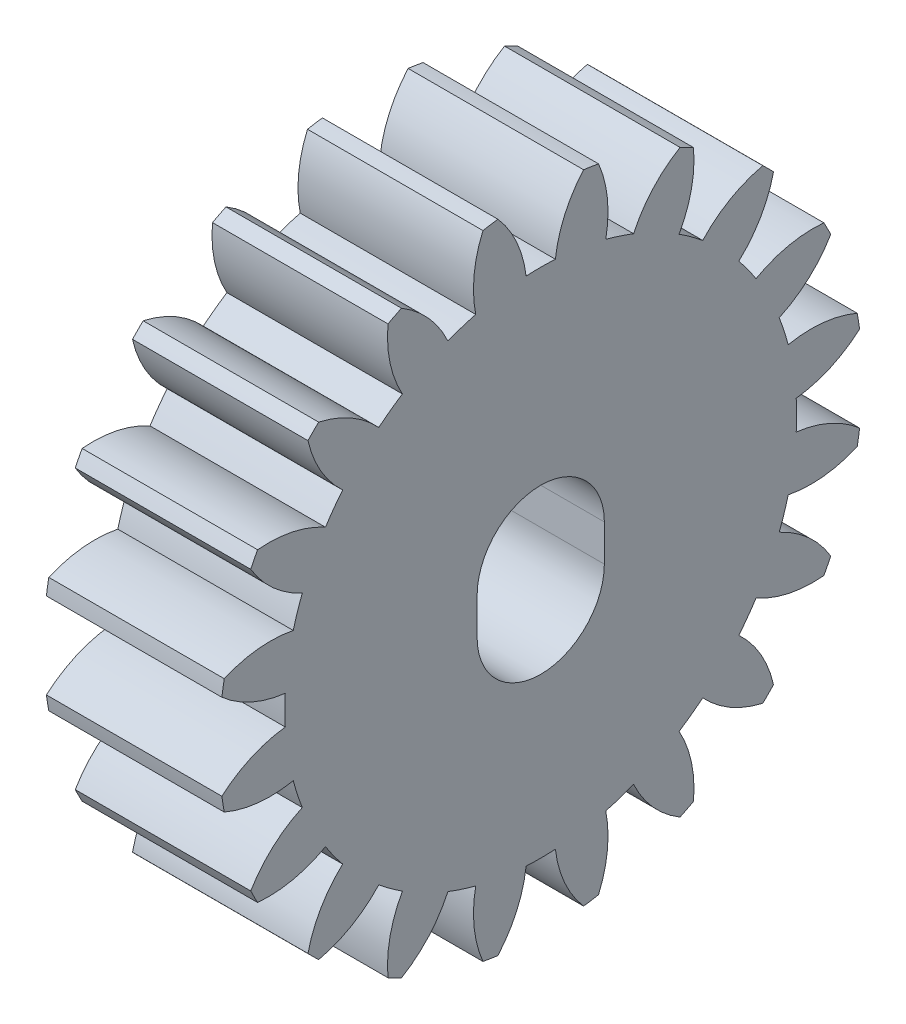
SolidWorks part; units mm, degrees
ref_plane "Спереди" through (0, 0, 0) normal (0, 0, 1) x (1, 0, 0)
ref_plane "Сверху" through (0, 0, 0) normal (0, 1, 0) x (1, 0, 0)
ref_plane "Справа" through (0, 0, 0) normal (1, 0, 0) x (0, 0, -1)
ref_plane "Плоскость4" through (0.2049, 0, 0) normal (1, 0, 0) x (0, 0, -1)
sketch "Эскиз1" plane through (0.2049, 3.1521, 1.205) normal (1, 0, 0) x (0, 0, -1)
  line L0 (1.205, -3.0337) -> (1.205, -4.2837) construction
  line L3 (3.38, -3.0337) -> (3.38, -4.2837)
  line L4 (-0.97, -3.0337) -> (-0.97, -4.2837)
  arc A1 (-9.697, -1.6872) -> (-7.5297, -2.6522) centre (-7.0595, 1.3201) ccw
  arc A2 (-7.5297, -2.6522) -> (-7.5297, -3.6521) centre (1.205, -3.1521) ccw
  arc A3 (-7.5297, -3.6521) -> (-9.697, -4.6171) centre (-7.0595, -7.6243) ccw
  arc A4 (-9.697, -4.6171) -> (-9.6161, -5.1278) centre (1.205, -3.1521) ccw
  arc A5 (-9.6161, -5.1278) -> (-7.2567, -5.3758) centre (-8.0369, -1.4527) ccw
  arc A6 (-7.2567, -5.3758) -> (-6.9477, -6.3268) centre (1.205, -3.1521) ccw
  arc A7 (-6.9477, -6.3268) -> (-8.7107, -7.9143) centre (-5.273, -9.9593) ccw
  arc A8 (-8.7107, -7.9143) -> (-8.476, -8.375) centre (1.205, -3.1521) ccw
  arc A9 (-8.476, -8.375) -> (-6.1553, -7.8818) centre (-8.1098, -4.3918) ccw
  arc A10 (-6.1553, -7.8818) -> (-5.5676, -8.6907) centre (1.205, -3.1521) ccw
  arc A11 (-5.5676, -8.6907) -> (-6.7538, -10.7453) centre (-2.8524, -11.6279) ccw
  arc A12 (-6.7538, -10.7453) -> (-6.3882, -11.111) centre (1.205, -3.1521) ccw
  arc A13 (-6.3882, -11.111) -> (-4.3335, -9.9248) centre (-7.2708, -7.2095) ccw
  arc A14 (-4.3335, -9.9248) -> (-3.5247, -10.5125) centre (1.205, -3.1521) ccw
  arc A15 (-3.5247, -10.5125) -> (-4.0178, -12.8331) centre (-0.0346, -12.4669) ccw
  arc A16 (-4.0178, -12.8331) -> (-3.5571, -13.0679) centre (1.205, -3.1521) ccw
  arc A17 (-3.5571, -13.0679) -> (-1.9696, -11.3048) centre (-5.6021, -9.6301) ccw
  arc A18 (-1.9696, -11.3048) -> (-1.0187, -11.6138) centre (1.205, -3.1521) ccw
  arc A19 (-1.0187, -11.6138) -> (-0.7706, -13.9733) centre (2.9045, -12.3941) ccw
  arc A20 (-0.7706, -13.9733) -> (-0.2599, -14.0541) centre (1.205, -3.1521) ccw
  arc A21 (-0.2599, -14.0541) -> (0.7051, -11.8868) centre (-3.2672, -11.4166) ccw
  arc A22 (0.7051, -11.8868) -> (1.705, -11.8868) centre (1.205, -3.1521) ccw
  arc A23 (1.705, -11.8868) -> (2.67, -14.0541) centre (5.6772, -11.4166) ccw
  arc A24 (2.67, -14.0541) -> (3.1807, -13.9733) centre (1.205, -3.1521) ccw
  arc A25 (3.1807, -13.9733) -> (3.4287, -11.6138) centre (-0.4944, -12.3941) ccw
  arc A26 (3.4287, -11.6138) -> (4.3797, -11.3048) centre (1.205, -3.1521) ccw
  arc A27 (4.3797, -11.3048) -> (5.9672, -13.0679) centre (8.0122, -9.6301) ccw
  arc A28 (5.9672, -13.0679) -> (6.4279, -12.8331) centre (1.205, -3.1521) ccw
  arc A29 (6.4279, -12.8331) -> (5.9347, -10.5125) centre (2.4447, -12.4669) ccw
  arc A30 (5.9347, -10.5125) -> (6.7436, -9.9248) centre (1.205, -3.1521) ccw
  arc A31 (6.7436, -9.9248) -> (8.7982, -11.111) centre (9.6809, -7.2095) ccw
  arc A32 (8.7982, -11.111) -> (9.1639, -10.7453) centre (1.205, -3.1521) ccw
  arc A33 (9.1639, -10.7453) -> (7.9777, -8.6907) centre (5.2625, -11.6279) ccw
  arc A34 (7.9777, -8.6907) -> (8.5654, -7.8818) centre (1.205, -3.1521) ccw
  arc A35 (8.5654, -7.8818) -> (10.886, -8.375) centre (10.5198, -4.3918) ccw
  arc A36 (10.886, -8.375) -> (11.1208, -7.9143) centre (1.205, -3.1521) ccw
  arc A37 (11.1208, -7.9143) -> (9.3577, -6.3268) centre (7.683, -9.9593) ccw
  arc A38 (9.3577, -6.3268) -> (9.6667, -5.3758) centre (1.205, -3.1521) ccw
  arc A39 (9.6667, -5.3758) -> (12.0262, -5.1278) centre (10.447, -1.4527) ccw
  arc A40 (12.0262, -5.1278) -> (12.107, -4.6171) centre (1.205, -3.1521) ccw
  arc A41 (12.107, -4.6171) -> (9.9397, -3.6521) centre (9.4695, -7.6243) ccw
  arc A42 (9.9397, -3.6521) -> (9.9397, -2.6522) centre (1.205, -3.1521) ccw
  arc A43 (9.9397, -2.6522) -> (12.107, -1.6872) centre (9.4695, 1.3201) ccw
  arc A44 (12.107, -1.6872) -> (12.0262, -1.1765) centre (1.205, -3.1521) ccw
  arc A45 (12.0262, -1.1765) -> (9.6667, -0.9284) centre (10.447, -4.8516) ccw
  arc A46 (9.6667, -0.9284) -> (9.3577, 0.0225) centre (1.205, -3.1521) ccw
  arc A47 (9.3577, 0.0225) -> (11.1208, 1.61) centre (7.683, 3.655) ccw
  arc A48 (11.1208, 1.61) -> (10.886, 2.0707) centre (1.205, -3.1521) ccw
  arc A49 (10.886, 2.0707) -> (8.5654, 1.5776) centre (10.5198, -1.9125) ccw
  arc A50 (8.5654, 1.5776) -> (7.9777, 2.3865) centre (1.205, -3.1521) ccw
  arc A51 (7.9777, 2.3865) -> (9.1639, 4.4411) centre (5.2625, 5.3237) ccw
  arc A52 (9.1639, 4.4411) -> (8.7982, 4.8067) centre (1.205, -3.1521) ccw
  arc A53 (8.7982, 4.8067) -> (6.7436, 3.6206) centre (9.6809, 0.9053) ccw
  arc A54 (6.7436, 3.6206) -> (5.9347, 4.2082) centre (1.205, -3.1521) ccw
  arc A55 (5.9347, 4.2082) -> (6.4279, 6.5289) centre (2.4447, 6.1627) ccw
  arc A56 (6.4279, 6.5289) -> (5.9672, 6.7636) centre (1.205, -3.1521) ccw
  arc A57 (5.9672, 6.7636) -> (4.3797, 5.0006) centre (8.0122, 3.3259) ccw
  arc A58 (4.3797, 5.0006) -> (3.4287, 5.3096) centre (1.205, -3.1521) ccw
  arc A59 (3.4287, 5.3096) -> (3.1807, 7.669) centre (-0.4944, 6.0899) ccw
  arc A60 (3.1807, 7.669) -> (2.67, 7.7499) centre (1.205, -3.1521) ccw
  arc A61 (2.67, 7.7499) -> (1.705, 5.5826) centre (5.6772, 5.1124) ccw
  arc A62 (1.705, 5.5826) -> (0.7051, 5.5826) centre (1.205, -3.1521) ccw
  arc A63 (0.7051, 5.5826) -> (-0.2599, 7.7499) centre (-3.2672, 5.1124) ccw
  arc A64 (-0.2599, 7.7499) -> (-0.7706, 7.669) centre (1.205, -3.1521) ccw
  arc A65 (-0.7706, 7.669) -> (-1.0187, 5.3096) centre (2.9045, 6.0899) ccw
  arc A66 (-1.0187, 5.3096) -> (-1.9696, 5.0006) centre (1.205, -3.1521) ccw
  arc A67 (-1.9696, 5.0006) -> (-3.5571, 6.7636) centre (-5.6021, 3.3259) ccw
  arc A68 (-3.5571, 6.7636) -> (-4.0178, 6.5289) centre (1.205, -3.1521) ccw
  arc A69 (-4.0178, 6.5289) -> (-3.5247, 4.2082) centre (-0.0346, 6.1627) ccw
  arc A70 (-3.5247, 4.2082) -> (-4.3335, 3.6206) centre (1.205, -3.1521) ccw
  arc A71 (-4.3335, 3.6206) -> (-6.3882, 4.8067) centre (-7.2708, 0.9053) ccw
  arc A72 (-6.3882, 4.8067) -> (-6.7538, 4.4411) centre (1.205, -3.1521) ccw
  arc A73 (-6.7538, 4.4411) -> (-5.5676, 2.3865) centre (-2.8524, 5.3237) ccw
  arc A74 (-5.5676, 2.3865) -> (-6.1553, 1.5776) centre (1.205, -3.1521) ccw
  arc A75 (-6.1553, 1.5776) -> (-8.476, 2.0707) centre (-8.1098, -1.9125) ccw
  arc A76 (-8.476, 2.0707) -> (-8.7107, 1.61) centre (1.205, -3.1521) ccw
  arc A77 (-8.7107, 1.61) -> (-6.9477, 0.0225) centre (-5.273, 3.655) ccw
  arc A78 (-6.9477, 0.0225) -> (-7.2567, -0.9284) centre (1.205, -3.1521) ccw
  arc A79 (-7.2567, -0.9284) -> (-9.6161, -1.1765) centre (-8.0369, -4.8516) ccw
  arc A80 (-9.6161, -1.1765) -> (-9.697, -1.6872) centre (1.205, -3.1521) ccw
  arc A82 (3.38, -3.0337) -> (-0.97, -3.0337) centre (1.205, -3.0337) ccw
  arc A83 (-0.97, -4.2837) -> (3.38, -4.2837) centre (1.205, -4.2837) ccw
  point P124 (1.205, -3.6587)
  dimension "D1" = 18.7881
  dimension "D2" = 4.35
  dimension "D3" = 5.6
extrude "Бобышка-Вытянуть1" add sketch "Эскиз1" against normal blind 6
